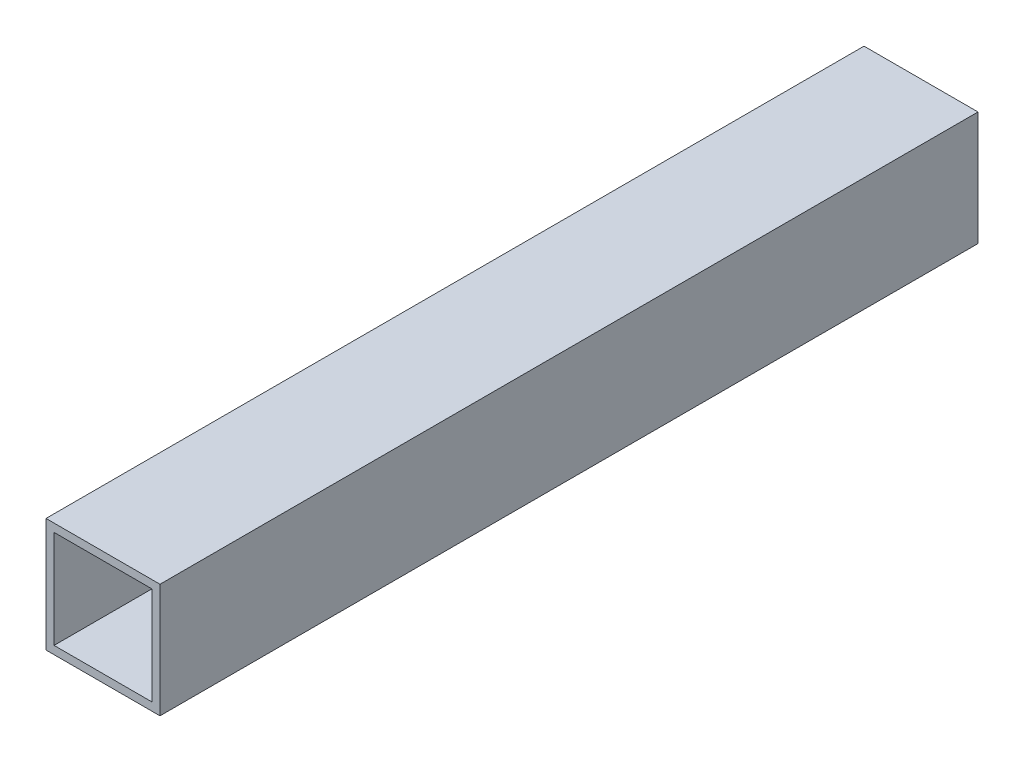
SolidWorks part; units mm, degrees
material "6061 Alloy"
ref_plane "Front Plane" through (0, 0, 0) normal (0, 0, 1) x (1, 0, 0)
ref_plane "Top Plane" through (0, 0, 0) normal (0, 1, 0) x (1, 0, 0)
ref_plane "Right Plane" through (0, 0, 0) normal (1, 0, 0) x (0, 0, -1)
sketch "Sketch1" plane through (0, 0, 0) normal (0, 0, 1) x (1, 0, 0)
  line L0 (-7.3, 7.3) -> (7.3, 7.3)
  line L1 (-8.5, -8.5) -> (8.5, -8.5)
  line L2 (-8.5, -8.5) -> (-8.5, 8.5)
  line L3 (-8.5, 8.5) -> (8.5, 8.5)
  line L4 (8.5, -8.5) -> (8.5, 8.5)
  line L5 (-8.5, -8.5) -> (8.5, 8.5) construction
  line L6 (-8.5, 8.5) -> (8.5, -8.5) construction
  line L7 (7.3, -7.3) -> (7.3, 7.3)
  line L8 (-7.3, -7.3) -> (7.3, -7.3)
  line L9 (-7.3, -7.3) -> (-7.3, 7.3)
  point P0 (0, 0)
  dimension "D1" = 17
  dimension "D2" = 17
  dimension "D3" = 1.2
extrude "Boss-Extrude1" add sketch "Sketch1" along normal blind 122
